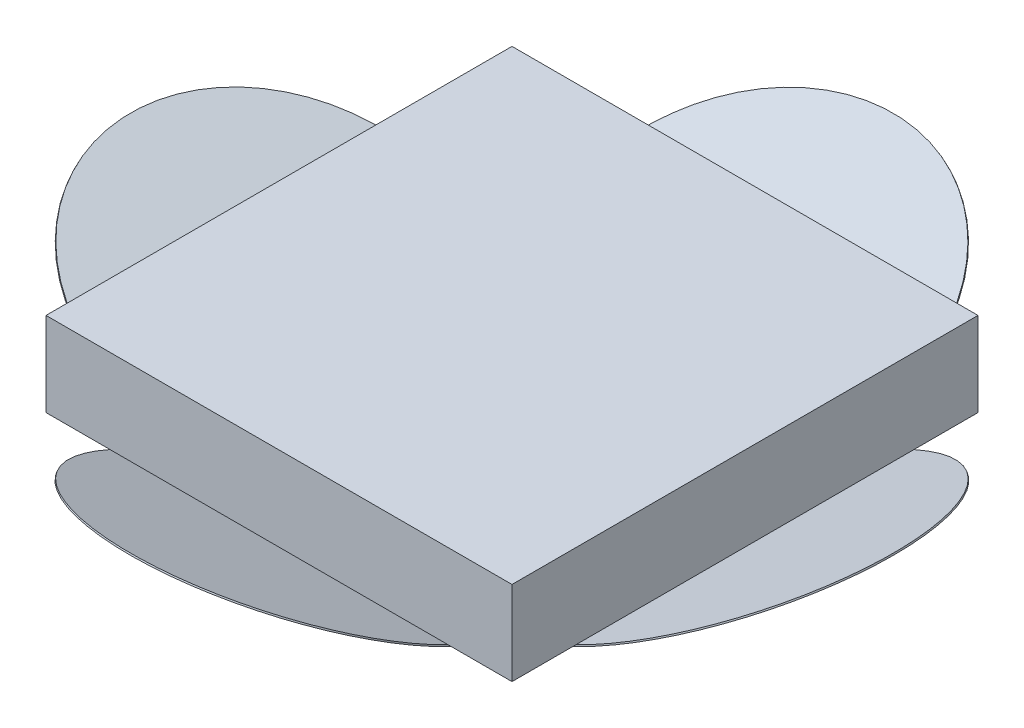
SolidWorks part; units mm, degrees
ref_plane "Alzado" through (0, 0, 0) normal (0, 0, 1) x (1, 0, 0)
ref_plane "Planta" through (0, 0, 0) normal (0, 1, 0) x (1, 0, 0)
ref_plane "Vista lateral" through (0, 0, 0) normal (1, 0, 0) x (0, 0, -1)
sketch "Croquis1" plane through (0, 0, 0) normal (0, 0, 1) x (1, 0, 0)
  line L0 (-51.9597, 8.9278) -> (-51.9597, 3.1482)
  line L1 (-51.9597, 8.9278) -> (-19.9597, 8.9278)
  line L2 (-19.9597, 8.9278) -> (-19.9597, 3.1482)
  line L3 (-19.9597, 3.1482) -> (-35.9597, -4.2902)
  line L4 (-35.9597, -4.2902) -> (-51.9597, 3.1482)
extrude "Saliente-Extruir1" add sketch "Croquis1" along normal blind 32
sketch "Croquis2" plane through (-19.9597, 0, 0) normal (1, 0, 0) x (0, 0, -1)
  line L5 (-32, 8.9278) -> (-32, 3.1482)
  line L6 (-32, 3.1482) -> (-16, -4.2902)
  line L7 (-32, -4.2902) -> (0, -4.2902) construction
  line L8 (-16, -4.2902) -> (-32, -4.2902)
  line L9 (-32, -4.2902) -> (-32, 3.1482)
  line L10 (-16, -4.2902) -> (0, 3.1482)
  line L11 (0, 3.1482) -> (0, -4.2902)
  line L12 (0, -4.2902) -> (-16, -4.2902)
extrude "Cortar-Extruir1" cut sketch "Croquis2" against normal blind 33 contours L12 L11 L10 | L9 L8 L6
sketch "Croquis3" plane through (-4.7507, 10.2188, 0) normal (0.4216, -0.9068, 0) x (-0.9068, -0.4216, 0)
  line L0 (16.7722, 0) -> (34.4167, -16) construction
  line L1 (34.4167, -16) -> (16.7722, -32) construction
  circle A0 centre (17.1415, -16) radius 11.6045
  dimension "D1" = 23.2089
extrude "Saliente-Extruir2" add sketch "Croquis3" along normal blind 0.1
sketch "Croquis4" plane through (0, -9.6442, 4.4836) normal (0, -0.9068, 0.4216) x (-1, 0, 0)
  line L0 (51.9597, -30.3447) -> (35.9597, -12.7001) construction
  line L1 (35.9597, -12.7001) -> (27.3632, -22.1801) construction
  circle A0 centre (35.9597, -29.9835) radius 11.61
extrude "Saliente-Extruir3" add sketch "Croquis4" along normal blind 0.1
sketch "Croquis6" plane through (-8.0308, -17.2743, 0) normal (-0.4216, -0.9068, 0) x (-0.9068, 0.4216, 0)
  line L0 (30.7995, -16) -> (48.444, 0) construction
  line L1 (40.284, -24.6005) -> (30.7995, -16) construction
  circle A0 centre (48.0716, -16) radius 11.6024
extrude "Saliente-Extruir4" add sketch "Croquis6" along normal blind 0.1
sketch "Croquis7" plane through (0, 2.5887, 1.2035) normal (0, -0.9068, -0.4216) x (-1, 0, 0)
  line L0 (35.9597, -16.3174) -> (44.5546, -6.839) construction
  line L1 (27.3632, -6.8374) -> (35.9597, -16.3174) construction
  circle A0 centre (35.9597, 0.9455) radius 11.5962
  point P2 (67.7177, -14.9523)
extrude "Saliente-Extruir5" add sketch "Croquis7" along normal blind 0.1
